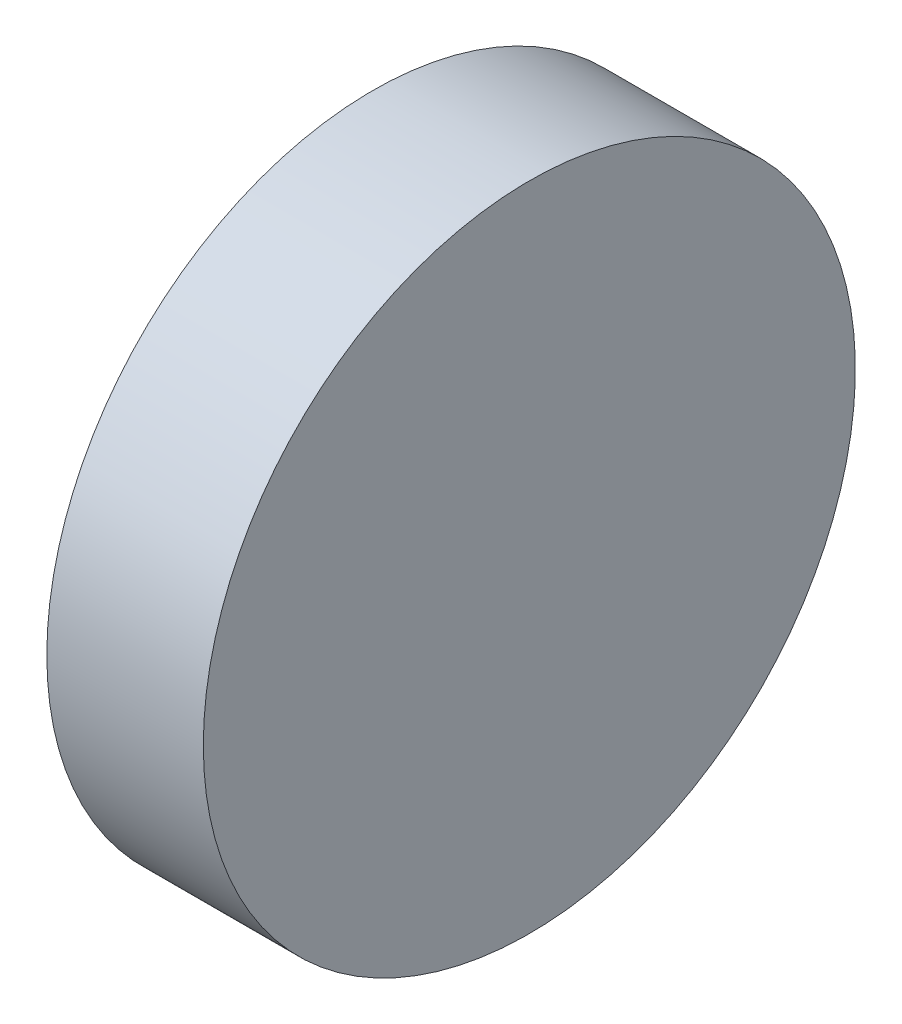
SolidWorks part; units mm, degrees
ref_plane "前视基准面" through (0, 0, 0) normal (0, 0, 1) x (1, 0, 0)
ref_plane "上视基准面" through (0, 0, 0) normal (0, 1, 0) x (1, 0, 0)
ref_plane "右视基准面" through (0, 0, 0) normal (1, 0, 0) x (0, 0, -1)
sketch "草图1" plane through (0, 0, 0) normal (0, 0, 1) x (1, 0, 0)
  line L0 (254.0008, 77.2932) -> (272.939, 77.2932) construction
  line L1 (260.2862, 77.2932) -> (260.2862, 89.7932)
  line L2 (266.2862, 77.2932) -> (266.2862, 89.7932)
  line L3 (260.2862, 77.2932) -> (266.2862, 77.2932)
  line L5 (260.2862, 89.7932) -> (266.2862, 89.7932)
  dimension "D1" = 6
  dimension "D2" = 12.5
revolve "旋转1" add sketch "草图1" angle 360 about L0
